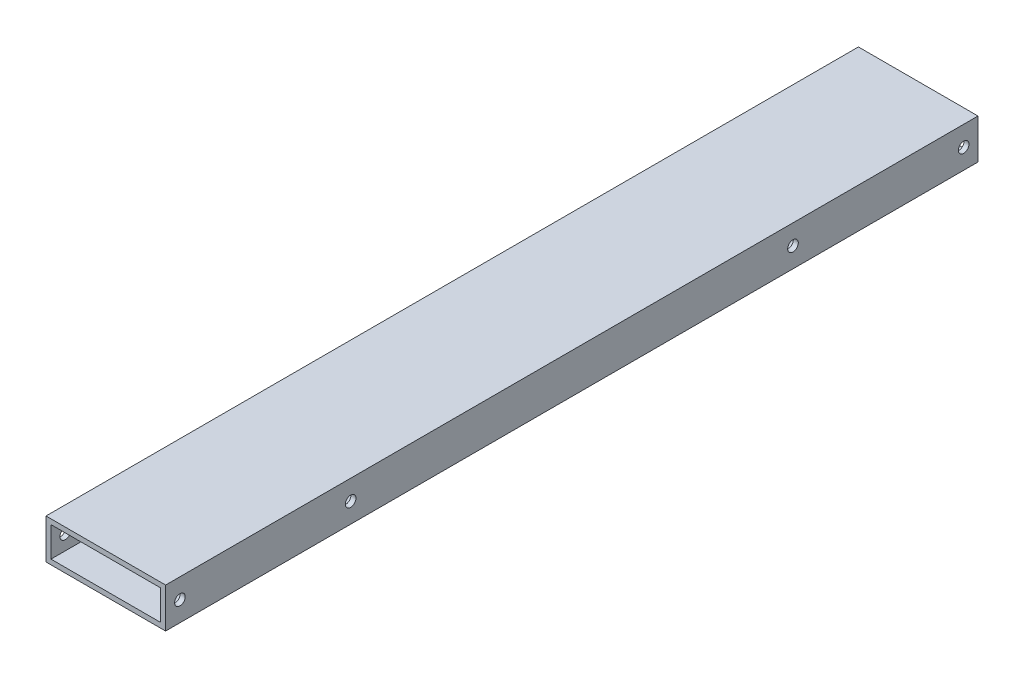
SolidWorks part; units mm, degrees
material "6061-T6 (SS)"
ref_plane "Front Plane" through (0, 0, 0) normal (0, 0, 1) x (1, 0, 0)
ref_plane "Top Plane" through (0, 0, 0) normal (0, 1, 0) x (1, 0, 0)
ref_plane "Right Plane" through (0, 0, 0) normal (1, 0, 0) x (0, 0, -1)
sketch "Sketch1" plane through (0, 0, 0) normal (0, 0, 1) x (1, 0, 0)
  line L0 (3.175, 22.225) -> (73.025, 22.225)
  line L1 (0, 0) -> (76.2, 0)
  line L2 (0, 0) -> (0, 25.4)
  line L3 (0, 25.4) -> (76.2, 25.4)
  line L4 (76.2, 0) -> (76.2, 25.4)
  line L5 (73.025, 3.175) -> (73.025, 22.225)
  line L6 (3.175, 3.175) -> (73.025, 3.175)
  line L7 (3.175, 3.175) -> (3.175, 22.225)
  dimension "D1" = 76.2
  dimension "D2" = 25.4
  dimension "D3" = 3.175
extrude "Boss-Extrude1" add sketch "Sketch1" along normal blind 517.525
ref_plane "Plane1" through (0, 0, 258.7625) normal (0, 0, -1) x (-1, 0, 0)
sketch "Sketch3" plane through (76.2, 0, 0) normal (1, 0, 0) x (0, 0, -1)
  circle A0 centre (-508.3937, 12.7) radius 3.3782
  circle A1 centre (-508.3937, 12.7) radius 3.3782 construction
  circle A2 centre (-399.6563, 12.7) radius 3.3782
  dimension "D1" = 6.7564
  dimension "D2" = 6.7564
  dimension "D3" = 0
extrude "Cut-Extrude1" cut sketch "Sketch3" against normal through all
mirror "Mirror1" about plane through (0, 0, 258.7625) normal (0, 0, -1) of "Cut-Extrude1"
